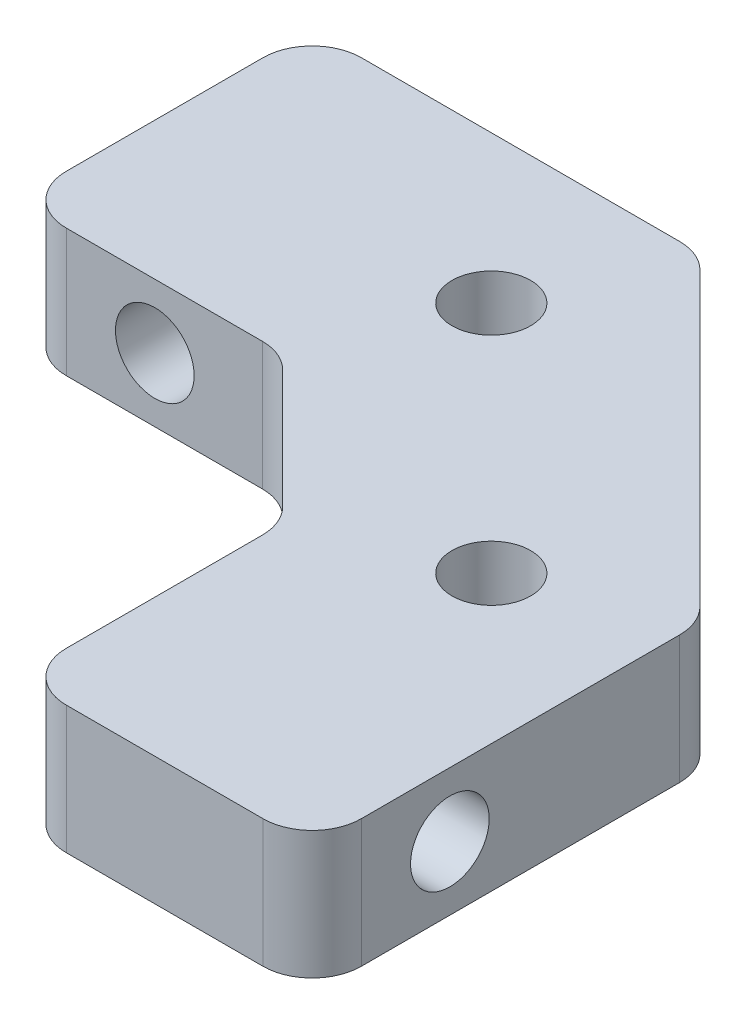
SolidWorks part; units mm, degrees
ref_plane "Front Plane" through (0, 0, 0) normal (0, 0, 1) x (1, 0, 0)
ref_plane "Top Plane" through (0, 0, 0) normal (0, 1, 0) x (1, 0, 0)
ref_plane "Right Plane" through (0, 0, 0) normal (1, 0, 0) x (0, 0, -1)
sketch "Sketch1" plane through (0, 0, 0) normal (0, 1, 0) x (1, 0, 0)
  line L1 (0, -15) -> (-15, 0)
  line L2 (0, -42) -> (30, -42)
  line L3 (-2.5736, 30) -> (30, -2.5736)
  line L4 (-42, 0) -> (-42, 30)
  line L5 (30, -2.5736) -> (30, -42)
  line L6 (-15, 0) -> (-42, 0)
  line L7 (0, -42) -> (0, -15)
  line L8 (-42, 30) -> (-2.5736, 30)
  circle A0 centre (-8.7868, 15) radius 4
  circle A1 centre (15, -8.7868) radius 4
extrude "Extrude1" add sketch "Sketch1" along normal blind 13
fillet "Fillet5" radius 5 8 edges at (0, 6.5, 42) (30, 6.5, 42) (30, 6.5, 2.5736) (-2.5736, 6.5, -30) (-42, 6.5, -30) (-42, 6.5, 0) (-15, 6.5, 0) (0, 6.5, 15)
sketch "Sketch5" plane through (-7.5, 0, 7.5) normal (-0.7071, 0, 0.7071) x (0.7071, 0, 0.7071)
  circle A0 centre (0, 6.5) radius 4
extrude "Extrude5" cut sketch "Sketch5" against normal blind 30
sketch "Sketch6" plane through (0, 0, 0) normal (0, 0, 1) x (1, 0, 0)
  circle A0 centre (-28, 6.5) radius 4
extrude "Extrude6" cut sketch "Sketch6" against normal blind 30
sketch "Sketch8" plane through (0, 0, 0) normal (-1, 0, 0) x (0, 0, 1)
  circle A0 centre (28, 6.5) radius 4
extrude "Extrude7" cut sketch "Sketch8" against normal blind 30
